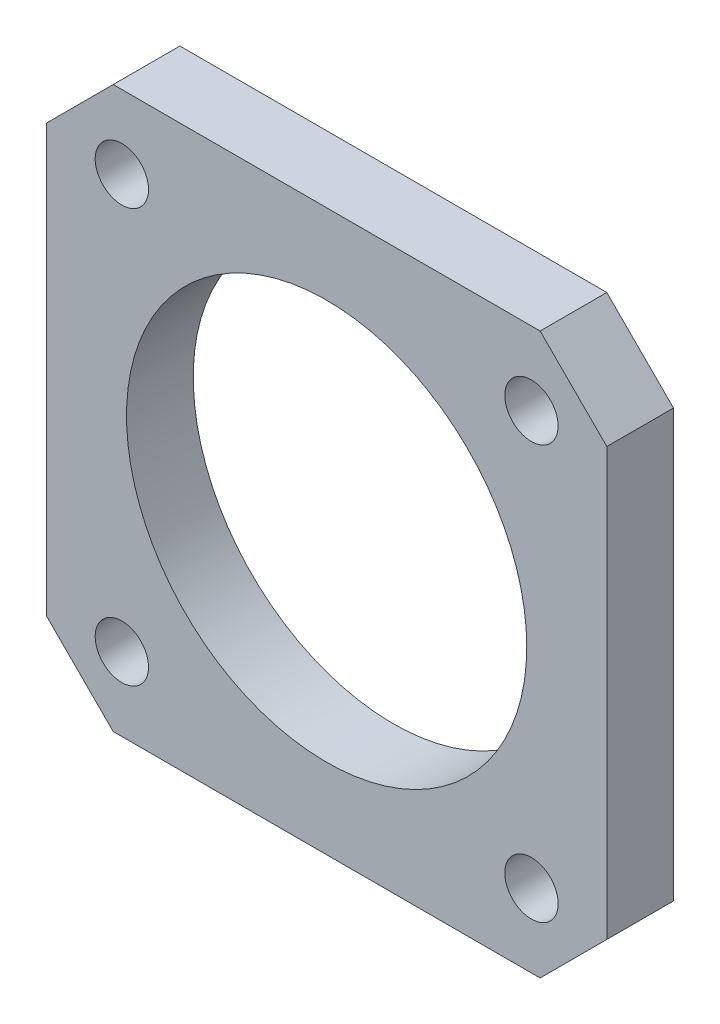
SolidWorks part; units mm, degrees
ref_plane "Front Plane" through (0, 0, 0) normal (0, 0, 1) x (1, 0, 0)
ref_plane "Top Plane" through (0, 0, 0) normal (0, 1, 0) x (1, 0, 0)
ref_plane "Right Plane" through (0, 0, 0) normal (1, 0, 0) x (0, 0, -1)
sketch "Sketch1" plane through (0, 0, 0) normal (0, 0, 1) x (1, 0, 0)
  line L1 (0, 0) -> (42, 0)
  line L2 (0, 0) -> (0, 42)
  line L3 (0, 42) -> (42, 42)
  line L4 (42, 0) -> (42, 42)
  dimension "D1" = 42
  dimension "D2" = 42
extrude "Boss-Extrude1" add sketch "Sketch1" along normal blind 5
sketch "Sketch2" plane through (0, 0, 5) normal (0, 0, 1) x (1, 0, 0)
  circle A0 centre (21, 21) radius 15
  dimension "D1" = 30
extrude "Cut-Extrude1" cut sketch "Sketch2" against normal through all
sketch "Sketch4" plane through (0, 0, 5) normal (0, 0, 1) x (1, 0, 0)
  line L0 (21, 21) -> (5.65, 21) construction
  line L1 (5.65, 21) -> (5.65, 36.5) construction
  line L2 (21, 21) -> (21, 36) construction
  circle A0 centre (5.65, 36.5) radius 2
  circle A1 centre (5.65, 5.5) radius 2
  circle A2 centre (21, 21) radius 15 construction
  circle A3 centre (36.35, 5.5) radius 2
  circle A4 centre (36.35, 36.5) radius 2
  dimension "D3" = 4
  dimension "D1" = 15.35
  dimension "D2" = 15.5
extrude "Cut-Extrude3" cut sketch "Sketch4" against normal blind 5
chamfer "Chamfer1" distance 5 angle 45 4 edges at (42, 0, 2.5) (0, 0, 2.5) (0, 42, 2.5) (42, 42, 2.5)
